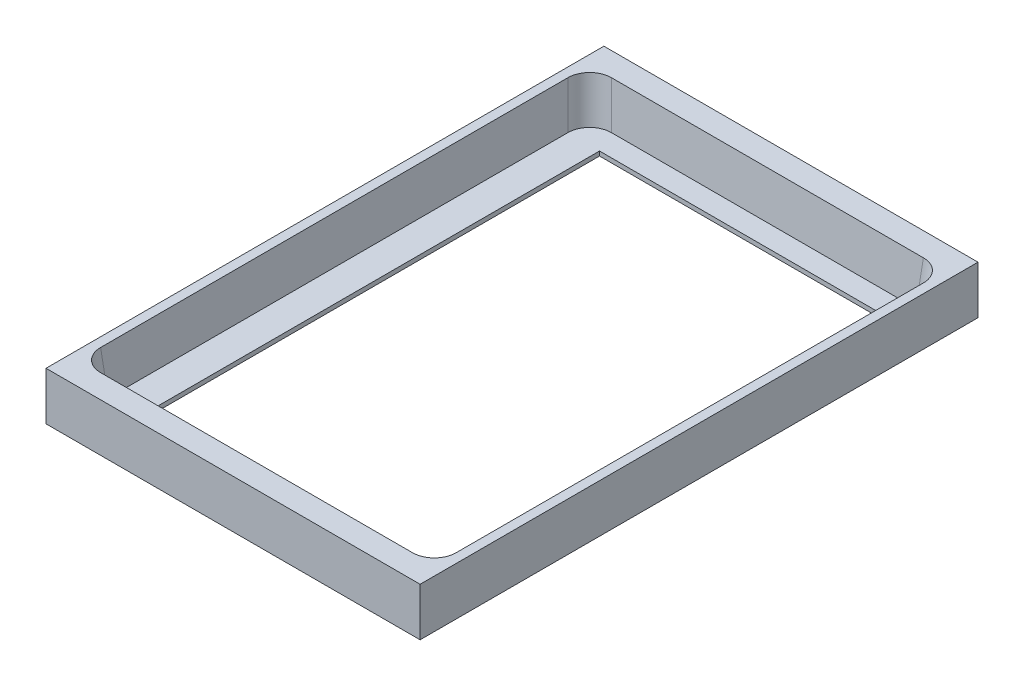
SolidWorks part; units mm, degrees
ref_plane "Front Plane" through (0, 0, 0) normal (0, 0, 1) x (1, 0, 0)
ref_plane "Top Plane" through (0, 0, 0) normal (0, 1, 0) x (1, 0, 0)
ref_plane "Right Plane" through (0, 0, 0) normal (1, 0, 0) x (0, 0, -1)
sketch "Sketch1" plane through (0, 0, 0) normal (0, 1, 0) x (1, 0, 0)
  line L1 (-42.75, 63.75) -> (42.75, 63.75)
  line L2 (-42.75, 63.75) -> (-42.75, -63.75)
  line L3 (-42.75, -63.75) -> (42.75, -63.75)
  line L4 (42.75, 63.75) -> (42.75, -63.75)
  line L5 (-42.75, 63.75) -> (42.75, -63.75) construction
  line L6 (-42.75, -63.75) -> (42.75, 63.75) construction
  point P0 (0, 0)
  dimension "D1" = 127.5
  dimension "D2" = 85.5
extrude "Boss-Extrude1" add sketch "Sketch1" along normal blind 10
sketch "Sketch2" plane through (0, 0, 0) normal (0, -1, 0) x (1, 0, 0)
  line L1 (39.75, -57.5) -> (-39.75, -57.5)
  line L2 (39.75, -57.5) -> (39.75, 57.5)
  line L3 (39.75, 57.5) -> (-39.75, 57.5)
  line L4 (-39.75, -57.5) -> (-39.75, 57.5)
  line L5 (39.75, -57.5) -> (-39.75, 57.5) construction
  line L6 (39.75, 57.5) -> (-39.75, -57.5) construction
  point P0 (0, 0)
  dimension "D1" = 115
  dimension "D2" = 79.5
extrude "Cut-Extrude1" cut sketch "Sketch2" along direction (0, 1, 0) on the side against the normal blind 10 draft 5 contours L2 L1 L4 L3
sketch "Sketch4" plane through (0, 0, 0) normal (0, -1, 0) x (1, 0, 0)
  line L1 (42.75, 63.75) -> (-42.75, 63.75)
  line L2 (42.75, 63.75) -> (42.75, -63.75)
  line L3 (42.75, -63.75) -> (-42.75, -63.75)
  line L4 (-42.75, 63.75) -> (-42.75, -63.75)
  line L5 (42.75, 63.75) -> (-42.75, -63.75) construction
  line L6 (42.75, -63.75) -> (-42.75, 63.75) construction
  point P0 (0, 0)
  dimension "D1" = 85.5
  dimension "D2" = 127.5
extrude "Boss-Extrude3" add sketch "Sketch4" along normal blind 1
sketch "Sketch6" plane through (0, -1, 0) normal (0, -1, 0) x (1, 0, 0)
  line L1 (32.5, -52.5) -> (-32.5, -52.5)
  line L2 (32.5, -52.5) -> (32.5, 52.5)
  line L3 (32.5, 52.5) -> (-32.5, 52.5)
  line L4 (-32.5, -52.5) -> (-32.5, 52.5)
  line L5 (32.5, -52.5) -> (-32.5, 52.5) construction
  line L6 (32.5, 52.5) -> (-32.5, -52.5) construction
  point P0 (0, 0)
  dimension "D1" = 65
  dimension "D2" = 105
extrude "Cut-Extrude2" cut sketch "Sketch6" against normal blind 1.1
fillet "Fillet2" radius 5 1 edges at (40.1874, 5, 57.9374)
fillet "Fillet3" radius 5 1 edges at (-40.1874, 5, 57.9374)
fillet "Fillet4" radius 5 1 edges at (-40.1874, 5, -57.9374)
fillet "Fillet5" radius 5 1 edges at (40.1874, 5, -57.9374)
